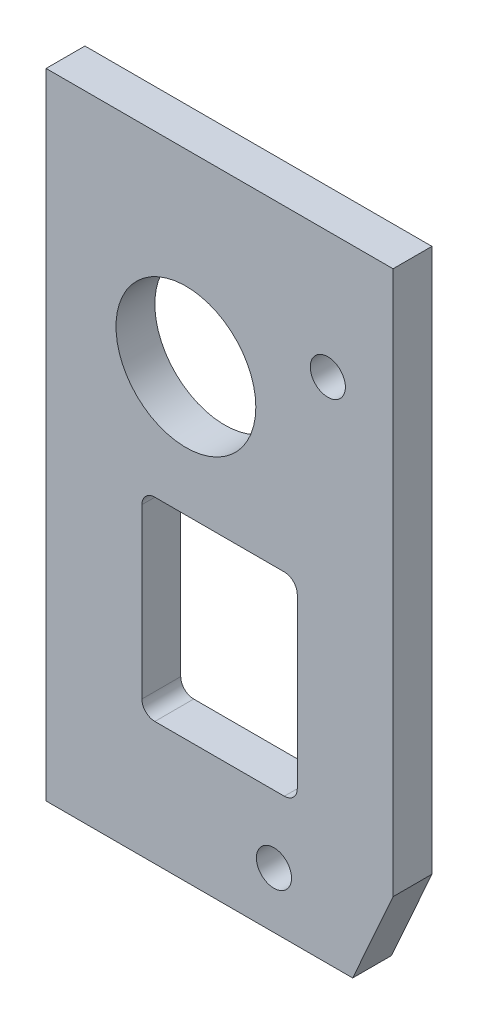
SolidWorks part; units mm, degrees
ref_plane "Front Plane" through (0, 0, 0) normal (0, 0, 1) x (1, 0, 0)
ref_plane "Top Plane" through (0, 0, 0) normal (0, 1, 0) x (1, 0, 0)
ref_plane "Right Plane" through (0, 0, 0) normal (1, 0, 0) x (0, 0, -1)
sketch "Sketch1" plane through (0, 0, 0) normal (0, 0, 1) x (1, 0, 0)
  line L5 (1.5875, -17.78) -> (1.5875, -95.5675)
  line L6 (1.5875, -95.5675) -> (39.1795, -95.5675)
  line L7 (39.1795, -95.5675) -> (44.1325, -84.455)
  line L8 (44.1325, -84.455) -> (44.1325, -17.78)
  line L9 (44.1325, -17.78) -> (1.5875, -17.78)
  line L10 (1.5875, -17.78) -> (1.5875, -95.5675)
  line L11 (1.5875, -95.5675) -> (39.1795, -95.5675)
  line L12 (39.1795, -95.5675) -> (44.1325, -84.455)
  line L13 (44.1325, -84.455) -> (44.1325, -17.78)
  line L14 (44.1325, -17.78) -> (1.5875, -17.78)
  line L15 (13.335, -56.642) -> (13.335, -80.4545)
  line L16 (32.385, -56.642) -> (13.335, -56.642)
  line L17 (32.385, -80.4545) -> (32.385, -56.642)
  line L18 (13.335, -80.4545) -> (32.385, -80.4545)
  line L19 (13.335, -56.642) -> (13.335, -80.4545)
  line L20 (32.385, -56.642) -> (13.335, -56.642)
  line L21 (32.385, -80.4545) -> (32.385, -56.642)
  line L22 (13.335, -80.4545) -> (32.385, -80.4545)
  dimension "D1" = 0
  dimension "D2" = 0
extrude "Boss-Extrude1" add sketch "Sketch1" along normal blind 4.7625
sketch "Sketch6" plane through (156.4061, -462.3851, 4.7625) normal (0, 0, 1) x (1, 0, 0)
  circle A0 centre (-137.6736, 421.4911) radius 8.5725
  dimension "D1" = 17.145
extrude "Cut-Extrude4" cut sketch "Sketch6" against normal through all
other "Smart-Feature1<SxAL-1>"
hole_wizard "#6 Clearance Hole1" positions "Sketch8" profile "Sketch7" hole size "#6" standard "ANSI Inch" end condition through all
sketch "Sketch8" plane through (0, 0, 4.7625) normal (0, 0, 1) x (1, 0, 0)
  point P0 (36.1315, -33.274)
  point P2 (29.5275, -88.7095)
sketch "Sketch7" plane through (36.1315, -33.274, 4.7625) normal (1, 0, 0) x (0, -1, 0)
  line L0 (0, 0) -> (0, 4.7625)
  line L1 (0, 4.7625) -> (2.1526, 4.7625)
  line L2 (2.1526, 4.7625) -> (2.1526, 0)
  line L5 (2.1526, 0) -> (0, 0)
  line L11 (0, -6.35) -> (0, 107.95) construction
  dimension "Thru Hole Dia." = 4.3053
  dimension "Thru Hole Depth" = 4.7625
fillet "Fillet1" radius 1.5875 4 edges at (13.335, -56.642, 2.3813) (13.335, -80.4545, 2.3813) (32.385, -80.4545, 2.3813) (32.385, -56.642, 2.3813)
